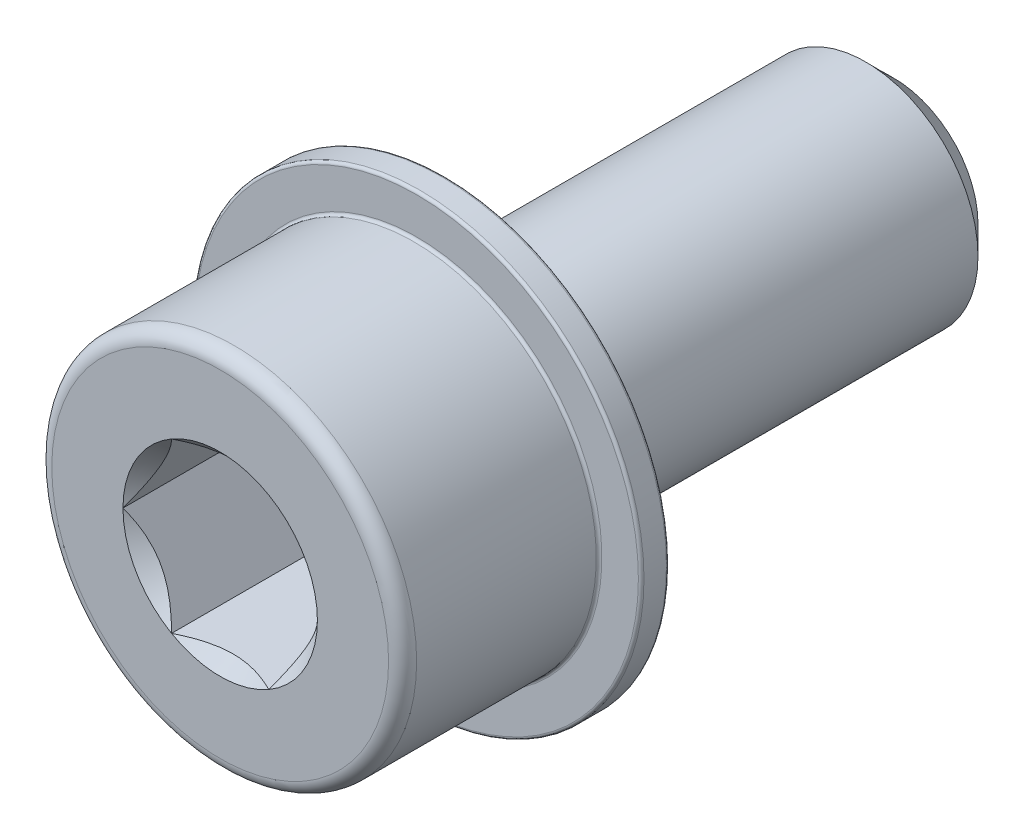
SolidWorks part; units mm, degrees
material "Acciaio inossidabile (ferroso)"
ref_plane "Piano frontale" through (0, 0, 0) normal (0, 0, 1) x (1, 0, 0)
ref_plane "Piano superiore" through (0, 0, 0) normal (0, 1, 0) x (1, 0, 0)
ref_plane "Piano destro" through (0, 0, 0) normal (1, 0, 0) x (0, 0, -1)
sketch "Schizzo1" plane through (0, 0, 0) normal (0, 0, 1) x (1, 0, 0)
  circle A0 centre (0, 0) radius 4
  dimension "D1" = 8
extrude "Estrusione-Estrusione1" add sketch "Schizzo1" along normal blind 16
cosmetic thread "Filettatura cosmetica2" parameters "D2"=6.619
chamfer "Smusso1" distance 1 angle 45 1 edges at (4, 0, 0)
sketch "Schizzo6" plane through (0, 0, 16) normal (0, 0, 1) x (1, 0, 0)
  circle A0 centre (0, 0) radius 6.5
  dimension "D1" = 13
extrude "Estrusione-Estrusione3" add sketch "Schizzo6" along normal blind 8
sketch "Schizzo7" plane through (0, 0, 24) normal (0, 0, 1) x (1, 0, 0)
  line L1 (1.7321, 3) -> (-1.7321, 3)
  line L2 (-1.7321, 3) -> (-3.4641, 0)
  line L3 (-3.4641, 0) -> (-1.7321, -3)
  line L4 (-1.7321, -3) -> (1.7321, -3)
  line L5 (1.7321, -3) -> (3.4641, 0)
  line L6 (3.4641, 0) -> (1.7321, 3)
  circle A1 centre (0, 0) radius 3 construction
  dimension "D1" = 6
extrude "Taglio-Estrusione3" cut sketch "Schizzo7" against normal blind 6
sketch "Schizzo8" plane through (0, 0, 24) normal (0, 0, 1) x (1, 0, 0)
  circle A0 centre (0, 0) radius 3.4641
extrude "Taglio-Estrusione4" cut sketch "Schizzo8" against normal blind 1 draft 45
fillet "Raccordo1" radius 0.5 1 edges at (6.5, 0, 24)
sketch "Schizzo9" plane through (0, 0, 16) normal (0, 0, -1) x (-1, 0, 0)
  circle A0 centre (0, 0) radius 6.5
  circle A1 centre (0, 0) radius 8
  dimension "D1" = 13
  dimension "D2" = 16
extrude "Estrusione-Estrusione4" add sketch "Schizzo9" against normal blind 1
fillet "Raccordo2" radius 0.1 3 edges at (-8, 0, 17) (-6.5, 0, 17) (-8, 0, 16)
